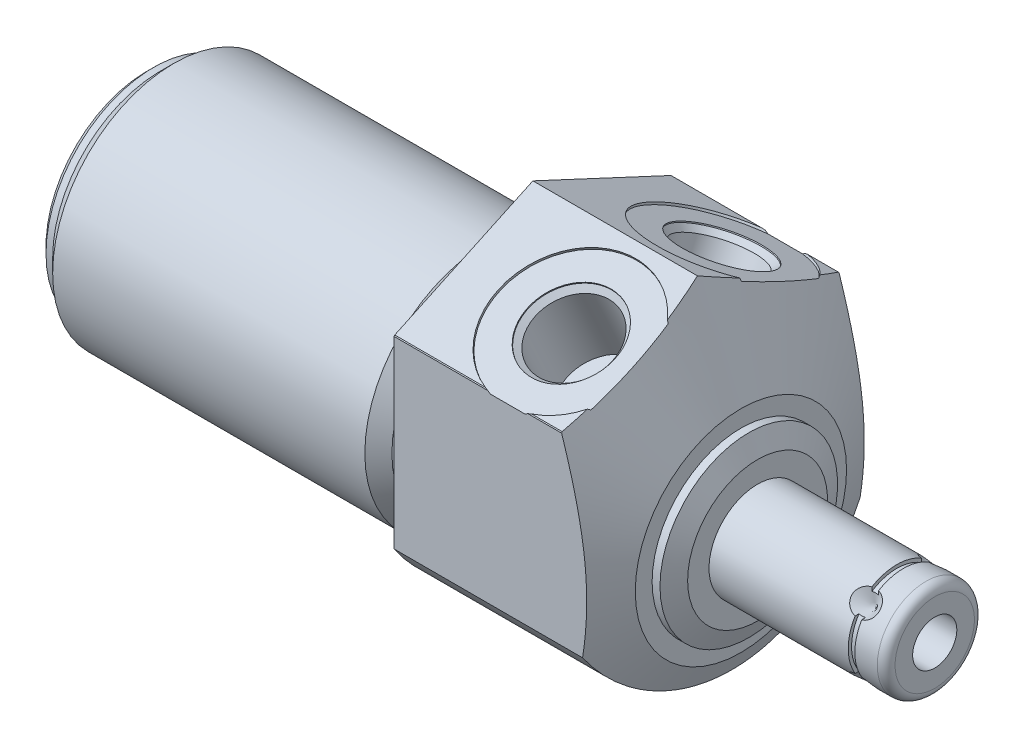
SolidWorks part; units mm, degrees
material "Alloy Steel"
ref_plane "Front Plane" through (0, 0, 0) normal (0, 0, 1) x (1, 0, 0)
ref_plane "Top Plane" through (0, 0, 0) normal (0, 1, 0) x (1, 0, 0)
ref_plane "Right Plane" through (0, 0, 0) normal (1, 0, 0) x (0, 0, -1)
sketch "Sketch1" plane through (0, 0, 0) normal (1, 0, 0) x (0, 0, -1)
  circle A0 centre (0, 0) radius 25.4
  dimension "D1" = 50.8
extrude "Extrude1" add sketch "Sketch1" along normal blind 25.7048 and the other way blind 44.1452
sketch "Sketch2" plane through (0, 0, 0) normal (1, 0, 0) x (0, 0, -1)
  line L0 (-14.6964, -4.7498) -> (14.6964, -4.7498) construction
  circle A0 centre (0, -4.7498) radius 13.8684
  circle A1 centre (0, 0) radius 25.4 construction
  circle A2 centre (0, 0) radius 25.4
  dimension "D1" = 27.7368
  dimension "D2" = 4.7498
extrude "Cut-Extrude1" cut sketch "Sketch2" against normal up to next
sketch "Sketch4" plane through (25.7048, 0, 0) normal (-1, 0, 0) x (0, 0, 1)
  line L0 (15.875, -10.5303) -> (15.875, 10.5303)
  line L1 (15.8029, 10.6381) -> (0, 18.0071)
  line L2 (-15.875, -10.5303) -> (-15.875, 10.5303)
  line L3 (-15.8029, 10.6381) -> (0, 18.0071)
  line L4 (0, -20.9029) -> (0, 19.86) construction
  circle A0 centre (0, 0) radius 25.4 construction
  circle A1 centre (0, 0) radius 25.4
  arc A2 (-15.8029, 10.6381) -> (-15.875, 10.5303) centre (0, 0) ccw
  arc A3 (-15.875, -10.5303) -> (15.875, -10.5303) centre (0, 0) ccw
  arc A4 (15.875, 10.5303) -> (15.8029, 10.6381) centre (0, 0) ccw
  dimension "D4" = 19.05
  dimension "D1" = 31.75
  dimension "D2" = 65
  dimension "D3" = 20.6248
extrude "Cut-Extrude3" cut sketch "Sketch4" along normal up to next
sketch "Sketch6" plane through (0, 0, 0) normal (0, 0, 1) x (1, 0, 0)
  line L0 (18.824, 18.0071) -> (23.7998, 7.3365)
  line L1 (1.9872, -4.7498) -> (19.8625, -4.7498) construction
  line L2 (-44.1452, -4.7498) -> (0, -4.7498) construction
  line L3 (25.7048, 18.0071) -> (25.7048, 10.6381) construction
  line L4 (25.7048, 3.2512) -> (25.7048, 18.0071)
  line L5 (25.7048, 18.0071) -> (18.824, 18.0071)
  line L6 (25.7048, 18.0071) -> (0, 18.0071) construction
  line L7 (23.7998, 7.3365) -> (23.7998, 5.4102)
  line L8 (23.7998, 5.4102) -> (24.698, 5.4102)
  line L9 (24.698, 5.4102) -> (25.7048, 3.2512)
  line L10 (0, 9.1186) -> (0, -18.6182) construction
  dimension "D1" = 16.002
  dimension "D2" = 25
  dimension "D3" = 20.32
  dimension "D4" = 23.7998
revolve "Cut-Revolve2" cut sketch "Sketch6" angle 360 about L1
ref_plane "Plane17" through (13.0048, 0, 0) normal (-1, 0, 0) x (0, 0, 1)
sketch "S2D0002" plane through (13.0048, 13.7124, 8.6091) normal (1, 0, 0) x (0, 0.4226, -0.9063)
  line L0 (5.0165, 0) -> (8.255, 0)
  line L1 (5.0165, 0) -> (5.0165, -0.127)
  line L2 (5.0165, -0.127) -> (4.4196, -0.7239)
  line L3 (4.4196, -0.7239) -> (4.4196, -9.398)
  line L4 (4.4196, -9.398) -> (0, -9.398)
  line L5 (0, -9.398) -> (0, 0.254)
  line L6 (0, -12.8016) -> (0, 0.6096) construction
  line L7 (8.255, 0.254) -> (8.255, 0)
  line L8 (9.6175, 0.254) -> (-7.8191, 0.254) construction
  line L9 (8.255, 0.254) -> (0, 0.254)
  dimension "D1" = 16.51
  dimension "D2" = 0.254
  dimension "D3" = 0.127
  dimension "D4" = 10.033
  dimension "D5" = 45
  dimension "D6" = 8.8392
  dimension "D7" = 9.398
revolve "Cut-Revolve3" cut sketch "S2D0002" angle 360 about L6
mirror "Mirror1" about plane through (0, 0, 0) normal (0, 0, 1) of "Cut-Revolve3"
sketch "Sketch10" plane through (0, 0, 0) normal (0, 0, 1) x (1, 0, 0)
  line L0 (0, 9.1186) -> (0, 7.5692)
  line L1 (0, 7.5692) -> (-3.81, 7.5692)
  line L2 (-3.81, 7.5692) -> (-5.3594, 9.1186)
  line L3 (-5.094, -4.7498) -> (0.2426, -4.7498) construction
  line L4 (0, 9.1186) -> (-5.3594, 9.1186)
  line L5 (-44.1452, -4.7498) -> (0, -4.7498) construction
  line L6 (0, 9.1186) -> (-44.1452, 9.1186) construction
  line L7 (0, 10.5303) -> (0, -10.5303) construction
  dimension "D1" = 24.638
  dimension "D2" = 3.81
  dimension "D3" = 45
revolve "Cut-Revolve6" cut sketch "Sketch10" angle 360 about L3
sketch "Sketch12" plane through (0, 0, 0) normal (0, 0, 1) x (1, 0, 0)
  line L0 (-44.1452, 9.1186) -> (-44.1452, 7.5692)
  line L1 (-44.1452, 7.5692) -> (-42.6212, 7.5692)
  line L2 (-42.6212, 7.5692) -> (-41.0718, 9.1186)
  line L3 (-50.9283, -4.7498) -> (-48.1063, -4.7498) construction
  line L4 (-44.1452, 9.1186) -> (-41.0718, 9.1186)
  line L5 (-44.1452, -4.7498) -> (-5.3594, -4.7498) construction
  line L6 (-5.3594, 9.1186) -> (-44.1452, 9.1186) construction
  line L7 (-44.1452, 9.1186) -> (-44.1452, -18.6182) construction
  dimension "D1" = 24.638
  dimension "D2" = 1.524
  dimension "D3" = 45
revolve "Cut-Revolve8" cut sketch "Sketch12" angle 360 about L3
chamfer "Chamfer1" distance 0.762 angle 45 1 edges at (-44.1452, -4.7498, 12.319)
sketch "Sketch13" plane through (0, 0, 0) normal (0, 0, 1) x (1, 0, 0)
  line L0 (25.7048, -4.7498) -> (45.974, -4.7498)
  line L1 (45.974, -4.7498) -> (45.974, -9.29)
  line L2 (44.958, -10.306) -> (25.7048, -10.306)
  line L3 (25.7048, -10.306) -> (25.7048, -4.7498)
  line L4 (4.7498, -4.7498) -> (27.0459, -4.7498) construction
  line L5 (-41.0718, -4.7498) -> (-5.3594, -4.7498) construction
  line L6 (25.7048, -12.7508) -> (25.7048, 3.2512) construction
  line L7 (0, 10.5303) -> (0, -10.5303) construction
  arc A0 (44.958, -10.306) -> (45.974, -9.29) centre (44.958, -9.29) ccw
  dimension "D2" = 1.016
  dimension "D1" = 45.974
  dimension "D3" = 11.1125
revolve "Revolve1" add sketch "Sketch13" angle 360 about L4
ref_plane "Plane18" through (0, -2.3749, -2.3749) normal (0, 0.7071, 0.7071) x (-1, 0, 0)
sketch "S2D0001" plane through (0, 0, 0) normal (0, 0, 1) x (1, 0, 0)
  line L0 (45.974, -2.2225) -> (35.814, -2.2225)
  line L1 (35.814, -2.2225) -> (34.2954, -4.7498)
  line L2 (45.974, -2.2225) -> (45.974, -4.7498)
  line L3 (45.974, -4.7498) -> (34.2954, -4.7498)
  line L4 (-2.8067, -4.7498) -> (-15.8378, -4.7498) construction
  line L5 (44.958, -4.7498) -> (25.7048, -4.7498) construction
  line L6 (45.974, -9.29) -> (45.974, -0.2096) construction
  dimension "D1" = 5.0546
  dimension "D2" = 10.16
  dimension "D3" = 59
revolve "Cut-Revolve9" cut sketch "S2D0001" angle 360 about L4
sketch "Sketch16" plane through (0, -8.1084, 3.3586) normal (0, -0.7071, -0.7071) x (1, 0, 0)
  line L0 (42.0116, -10.306) -> (40.4241, -10.306)
  line L1 (40.4241, -10.306) -> (42.0116, -8.7185)
  line L2 (42.0116, -10.306) -> (42.0116, -8.7185)
  line L3 (42.0116, -3.4788) -> (42.0116, 0.0794) construction
  line L4 (45.974, -9.2901) -> (45.974, -0.2096) construction
  line L5 (25.7048, -10.3061) -> (44.958, -10.3061) construction
  dimension "D1" = 3.9624
  dimension "D2" = 3.175
  dimension "D3" = 45
revolve "Cut-Revolve10" cut sketch "Sketch16" angle 360 about L3
pattern_circular "CirPattern1" count 4 over 360 about axis through (4.7498, -4.7498, 0) along (-1, 0, 0) of "Cut-Revolve10"
sketch "Sketch21" plane through (0, 0, 0) normal (0, 0, 1) x (1, 0, 0)
  line L1 (41.6306, 0.8065) -> (42.3926, 0.8065)
  line L2 (41.6306, 0.8065) -> (41.6306, 0.4255)
  line L3 (41.6306, 0.4255) -> (42.3926, 0.4255)
  line L4 (42.3926, 0.8065) -> (42.3926, 0.4255)
  line L5 (42.0116, -0.7782) -> (42.0116, 2.3032) construction
  line L7 (23.8735, -4.7498) -> (50.6625, -4.7498) construction
  line L10 (45.974, -9.29) -> (45.974, -0.2096) construction
  line L11 (19.534, -4.7498) -> (23.7998, -4.7498) construction
  dimension "D1" = 0.381
  dimension "D2" = 0.762
  dimension "D3" = 3.5814
  dimension "D4" = 5.5563
revolve "Cut-Revolve11" cut sketch "Sketch21" angle 360 about L7
